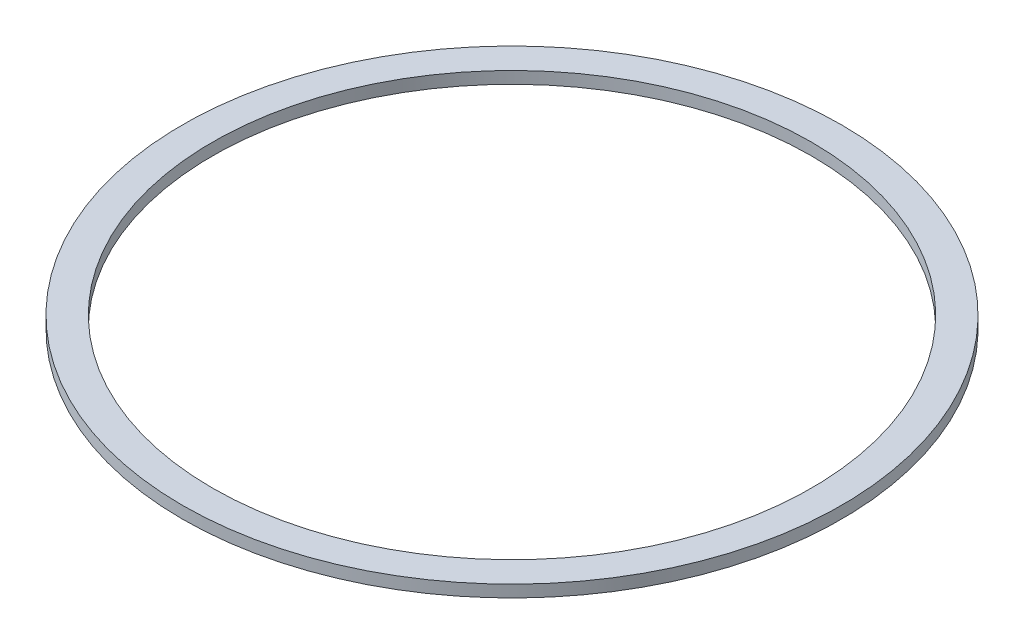
SolidWorks part; units mm, degrees
ref_plane "Front Plane" through (0, 0, 0) normal (0, 0, 1) x (1, 0, 0)
ref_plane "Top Plane" through (0, 0, 0) normal (0, 1, 0) x (1, 0, 0)
ref_plane "Right Plane" through (0, 0, 0) normal (1, 0, 0) x (0, 0, -1)
sketch "Sketch1" plane through (0, 0, 0) normal (0, 1, 0) x (1, 0, 0)
  circle A2 centre (0, 0) radius 82.5
  circle A3 centre (0, 0) radius 75
  dimension "D1" = 165
  dimension "D2" = 150
extrude "Boss-Extrude1" add sketch "Sketch1" along normal blind 3
